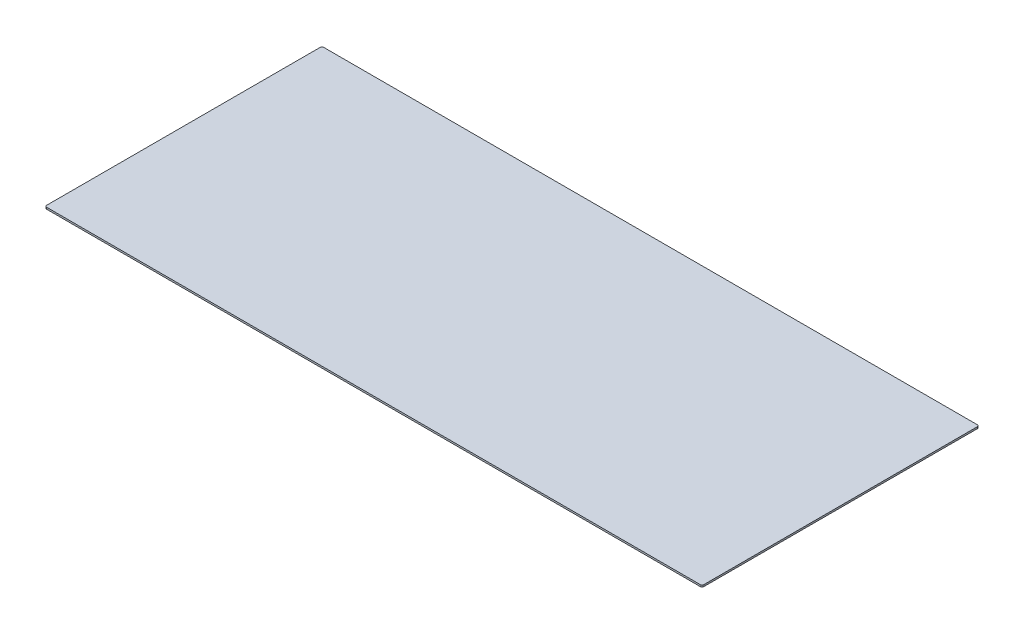
SolidWorks part; units mm, degrees
material "PE High Density"
ref_plane "Front Plane" through (0, 0, 0) normal (0, 0, 1) x (1, 0, 0)
ref_plane "Top Plane" through (0, 0, 0) normal (0, 1, 0) x (1, 0, 0)
ref_plane "Right Plane" through (0, 0, 0) normal (1, 0, 0) x (0, 0, -1)
sketch "Sketch1" plane through (0, 0, 0) normal (0, 1, 0) x (1, 0, 0)
  line L1 (-587.375, -248.92) -> (587.375, -248.92)
  line L2 (-590.55, -245.745) -> (-590.55, 245.745)
  line L3 (-587.375, 248.92) -> (587.375, 248.92)
  line L4 (590.55, -245.745) -> (590.55, 245.745)
  line L5 (-590.55, -248.92) -> (590.55, 248.92) construction
  line L6 (-590.55, 248.92) -> (590.55, -248.92) construction
  arc A0 (587.375, 248.92) -> (590.55, 245.745) centre (587.375, 245.745) cw
  arc A1 (587.375, -248.92) -> (590.55, -245.745) centre (587.375, -245.745) ccw
  arc A2 (-587.375, -248.92) -> (-590.55, -245.745) centre (-587.375, -245.745) cw
  arc A3 (-590.55, 245.745) -> (-587.375, 248.92) centre (-587.375, 245.745) cw
  point P0 (0, 0)
  dimension "D3" = 3.175
  dimension "D1" = 1181.1
  dimension "D2" = 497.84
extrude "Boss-Extrude1" add sketch "Sketch1" along normal blind 3.175
sketch "Sketch2" plane through (0, 3.175, 0) normal (0, 1, 0) x (1, 0, 0)
  line L0 (-590.55, 245.745) -> (-590.55, -245.745) construction
  line L1 (590.55, -245.745) -> (590.55, 245.745) construction
  line L2 (587.375, 248.92) -> (-587.375, 248.92) construction
  line L3 (-587.375, -248.92) -> (587.375, -248.92) construction
  point P0 (-406.4, 239.395)
  point P2 (0, 239.395)
  point P4 (406.4, 239.395)
  point P5 (-406.4, -239.395)
  point P7 (0, -239.395)
  point P9 (406.4, -239.395)
  point P16 (0, 106.045)
  point P17 (-317.5, 106.045)
  point P20 (317.5, 106.045)
  point P21 (-317.5, -150.495)
  point P24 (0, -150.495)
  point P25 (317.5, -150.495)
  dimension "D1" = 184.15
  dimension "D2" = 184.15
  dimension "D3" = 9.525
  dimension "D4" = 9.525
  dimension "D5" = 406.4
  dimension "D6" = 317.5
  dimension "D7" = 317.5
  dimension "D8" = 106.045
  dimension "D9" = 150.495
hole_wizard "1/4 (0.25) Diameter Hole1" [suppressed] positions "Sketch3" profile "Sketch4" hole size "1/4" standard "ANSI Inch"
sketch "Sketch3" plane through (0, 3.175, 0) normal (0, 1, 0) x (1, 0, 0)
  point P3 (-406.4, 239.395)
  point P9 (0, 239.395)
  point P15 (406.4, 239.395)
  point P27 (406.4, -239.395)
  point P33 (0, -239.395)
  point P39 (-406.4, -239.395)
sketch "Sketch4" plane through (-406.4, 3.175, -239.395) normal (1, 0, 0) x (0, 0, 1)
  line L0 (0, 0) -> (0, 3.175)
  line L1 (0, 3.175) -> (3.175, 3.175)
  line L2 (3.175, 3.175) -> (3.175, 0)
  line L5 (3.175, 0) -> (0, 0)
  line L11 (0, -6.35) -> (0, 107.95) construction
  dimension "Thru Hole Dia." = 6.35
  dimension "Thru Hole Depth" = 3.175
sketch "Sketch5" [suppressed] plane through (0, 3.175, 0) normal (0, 1, 0) x (1, 0, 0)
  line L0 (-419.1, 213.995) -> (-393.7, 213.995) construction
  line L1 (-419.1, 226.695) -> (-393.7, 226.695)
  line L2 (-419.1, 201.295) -> (-393.7, 201.295)
  line L6 (-12.7, 213.995) -> (12.7, 213.995) construction
  line L7 (-12.7, 226.695) -> (12.7, 226.695)
  line L8 (-12.7, 201.295) -> (12.7, 201.295)
  line L9 (590.55, -245.745) -> (590.55, 245.745) construction
  line L12 (393.7, 213.995) -> (419.1, 213.995) construction
  line L13 (393.7, 226.695) -> (419.1, 226.695)
  line L14 (393.7, 201.295) -> (419.1, 201.295)
  line L15 (-419.1, -213.995) -> (-393.7, -213.995) construction
  line L16 (-419.1, -201.295) -> (-393.7, -201.295)
  line L17 (-419.1, -226.695) -> (-393.7, -226.695)
  line L21 (-12.7, -213.995) -> (12.7, -213.995) construction
  line L22 (-12.7, -201.295) -> (12.7, -201.295)
  line L23 (-12.7, -226.695) -> (12.7, -226.695)
  line L27 (393.7, -213.995) -> (419.1, -213.995) construction
  line L28 (393.7, -201.295) -> (419.1, -201.295)
  line L29 (393.7, -226.695) -> (419.1, -226.695)
  line L31 (-590.55, 245.745) -> (-590.55, -245.745) construction
  arc A0 (-419.1, 226.695) -> (-419.1, 201.295) centre (-419.1, 213.995) ccw
  arc A1 (-393.7, 201.295) -> (-393.7, 226.695) centre (-393.7, 213.995) ccw
  arc A4 (-12.7, 226.695) -> (-12.7, 201.295) centre (-12.7, 213.995) ccw
  arc A5 (12.7, 201.295) -> (12.7, 226.695) centre (12.7, 213.995) ccw
  arc A8 (393.7, 226.695) -> (393.7, 201.295) centre (393.7, 213.995) ccw
  arc A9 (419.1, 201.295) -> (419.1, 226.695) centre (419.1, 213.995) ccw
  arc A10 (-419.1, -201.295) -> (-419.1, -226.695) centre (-419.1, -213.995) ccw
  arc A11 (-393.7, -226.695) -> (-393.7, -201.295) centre (-393.7, -213.995) ccw
  arc A14 (-12.7, -201.295) -> (-12.7, -226.695) centre (-12.7, -213.995) ccw
  arc A15 (12.7, -226.695) -> (12.7, -201.295) centre (12.7, -213.995) ccw
  arc A18 (393.7, -201.295) -> (393.7, -226.695) centre (393.7, -213.995) ccw
  arc A19 (419.1, -226.695) -> (419.1, -201.295) centre (419.1, -213.995) ccw
  circle A20 centre (-406.4, 239.395) radius 3.175 construction
  circle A21 centre (-406.4, -239.395) radius 3.175 construction
  circle A22 centre (0, 239.395) radius 3.175 construction
  circle A23 centre (406.4, 239.395) radius 3.175 construction
  circle A24 centre (406.4, -239.395) radius 3.175 construction
  point P2 (-406.4, 213.995)
  point P16 (0, 213.995)
  point P30 (406.4, 213.995)
  point P37 (-406.4, -213.995)
  point P51 (0, -213.995)
  point P65 (406.4, -213.995)
  dimension "D1" = 12.7
  dimension "D2" = 12.7
  dimension "D11" = 12.7
  dimension "D3" = 25.4
  dimension "D4" = 25.4
  dimension "D5" = 184.15
  dimension "D6" = 406.4
  dimension "D7" = 406.4
  dimension "D8" = 406.4
  dimension "D9" = 406.4
  dimension "D10" = 184.15
  dimension "D12" = 12.7
  dimension "D13" = 12.7
  dimension "D14" = 184.15
extrude "Cut-Extrude1" [suppressed] cut sketch "Sketch5" against normal through all
hole_wizard "#10 (0.1935) Diameter Hole7" [suppressed] positions "3DSketch2" profile "Sketch10" hole size "#10" standard "ANSI Inch"
sketch3d "3DSketch2"
  point P0 (-317.5, 3.175, -106.045)
  point P3 (0, 3.175, -106.045)
  point P12 (317.5, 3.175, -106.045)
  point P15 (317.5, 3.175, 150.495)
  point P18 (0, 3.175, 150.495)
  point P27 (-317.5, 3.175, 150.495)
sketch "Sketch10" plane through (-317.5, 3.175, -106.045) normal (1, 0, 0) x (0, 0, 1)
  line L0 (0, 0) -> (0, 3.175)
  line L1 (0, 3.175) -> (2.4574, 3.175)
  line L2 (2.4574, 3.175) -> (2.4574, 0)
  line L5 (2.4574, 0) -> (0, 0)
  line L11 (0, -6.35) -> (0, 107.95) construction
  dimension "Thru Hole Dia." = 4.9149
  dimension "Thru Hole Depth" = 3.175
sketch "Sketch11" plane through (0, 3.175, 0) normal (0, 1, 0) x (1, 0, 0)
  line L0 (-590.55, 245.745) -> (-590.55, -245.745) construction
  line L1 (-563.5625, 118.745) -> (563.5625, 118.745) construction
  line L2 (-563.5625, 118.745) -> (-563.5625, -163.195) construction
  line L3 (-563.5625, -163.195) -> (563.5625, -163.195) construction
  line L4 (563.5625, 118.745) -> (563.5625, -163.195) construction
  line L5 (-563.5625, 118.745) -> (563.5625, -163.195) construction
  line L6 (-563.5625, -163.195) -> (563.5625, 118.745) construction
  line L8 (563.5625, -137.795) -> (-563.5625, -137.795) construction
  line L9 (563.5625, -137.795) -> (563.5625, 93.345) construction
  line L10 (563.5625, 93.345) -> (-563.5625, 93.345) construction
  line L11 (-563.5625, -137.795) -> (-563.5625, 93.345) construction
  line L12 (563.5625, -137.795) -> (-563.5625, 93.345) construction
  line L13 (563.5625, 93.345) -> (-563.5625, -137.795) construction
  point P0 (0, -22.225)
  point P9 (0, -22.225)
  dimension "D1" = 26.9875
  dimension "D2" = 281.94
  dimension "D3" = 25.4
  dimension "D4" = 22.225
hole_wizard "17/64 (0.26563) Diameter Hole1" [suppressed] positions "Sketch12" profile "Sketch13" hole size "17/64" standard "ANSI Inch"
sketch "Sketch12" plane through (0, 3.175, 0) normal (0, 1, 0) x (1, 0, 0)
  point P0 (-563.5625, 118.745)
  point P3 (-563.5625, 93.345)
  point P6 (-563.5625, -137.795)
  point P9 (-563.5625, -163.195)
  point P12 (563.5625, -163.195)
  point P15 (563.5625, -137.795)
  point P18 (563.5625, 118.745)
  point P21 (563.5625, 93.345)
sketch "Sketch13" plane through (-563.5625, 3.175, -118.745) normal (1, 0, 0) x (0, 0, 1)
  line L0 (0, 0) -> (0, 3.175)
  line L1 (0, 3.175) -> (3.3735, 3.175)
  line L2 (3.3735, 3.175) -> (3.3735, 0)
  line L5 (3.3735, 0) -> (0, 0)
  line L11 (0, -6.35) -> (0, 107.95) construction
  dimension "Thru Hole Dia." = 6.747
  dimension "Thru Hole Depth" = 3.175
